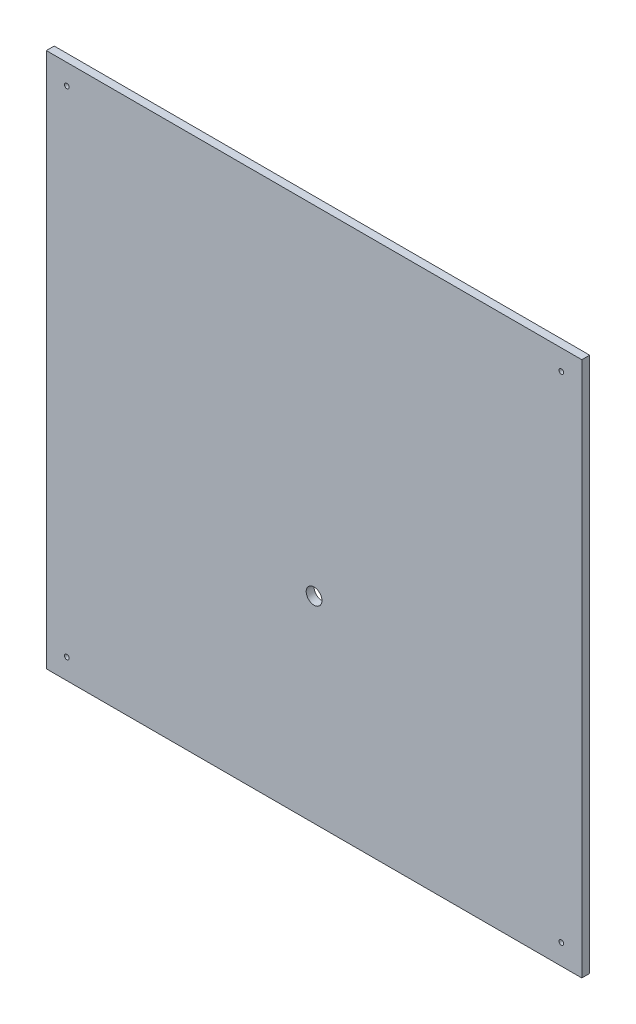
SolidWorks part; units mm, degrees
material "ABS"
ref_plane "Alzado" through (0, 0, 0) normal (0, 0, 1) x (1, 0, 0)
ref_plane "Planta" through (0, 0, 0) normal (0, 1, 0) x (1, 0, 0)
ref_plane "Vista lateral" through (0, 0, 0) normal (1, 0, 0) x (0, 0, -1)
sketch "Croquis1" plane through (0, 0, 0) normal (0, 0, 1) x (1, 0, 0)
  line L1 (-61.0528, 49.536) -> (278.9472, 49.536)
  line L2 (-61.0528, 49.536) -> (-61.0528, -290.464)
  line L3 (-61.0528, -290.464) -> (278.9472, -290.464)
  line L4 (278.9472, 49.536) -> (278.9472, -290.464)
  circle A0 centre (-48.0528, -277.464) radius 1.5
  circle A1 centre (-48.0528, 36.536) radius 1.5
  circle A2 centre (265.9472, -277.464) radius 1.5
  circle A3 centre (265.9472, 36.536) radius 1.5
  circle A4 centre (108.9472, -165.464) radius 5
  dimension "D3" = 13
  dimension "D11" = 170
  dimension "D1" = 340
  dimension "D2" = 340
  dimension "D4" = 13
  dimension "D5" = 13
  dimension "D6" = 13
  dimension "D7" = 13
  dimension "D8" = 13
  dimension "D9" = 13
  dimension "D10" = 13
  dimension "D12" = 125
extrude "Saliente-Extruir1" add sketch "Croquis1" along normal blind 5
